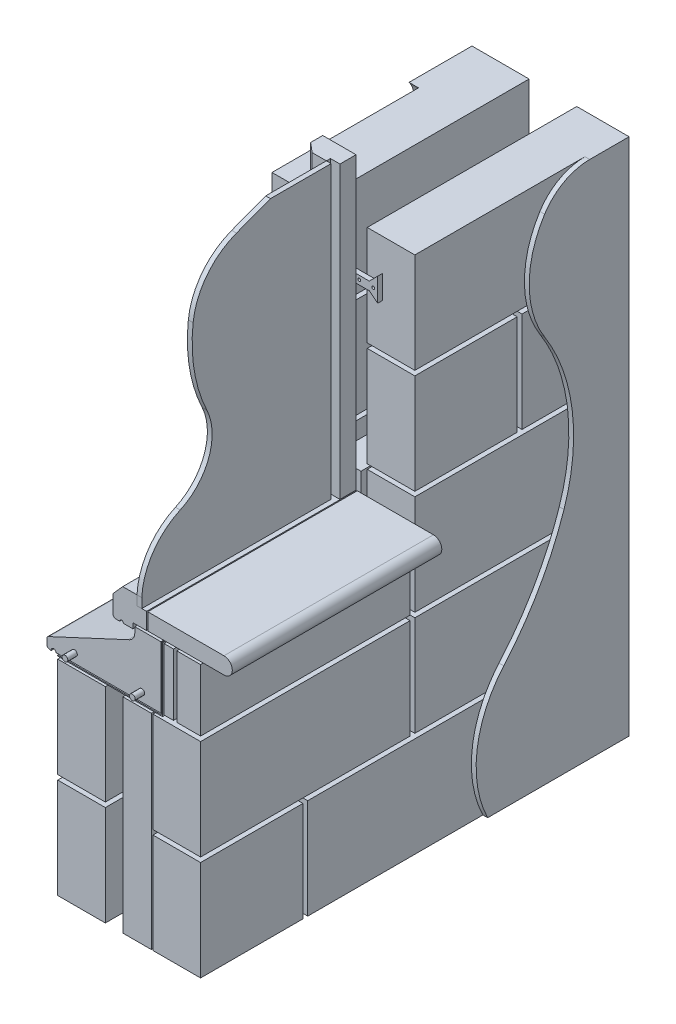
SolidWorks part; units mm, degrees
ref_plane "Front Plane" through (0, 0, 0) normal (0, 0, 1) x (1, 0, 0)
ref_plane "Top Plane" through (0, 0, 0) normal (0, 1, 0) x (1, 0, 0)
ref_plane "Right Plane" through (0, 0, 0) normal (1, 0, 0) x (0, 0, -1)
sketch "Sketch1" plane through (0, 0, 0) normal (0, 0, 1) x (1, 0, 0)
  line L1 (0, 0) -> (100, 0)
  line L2 (0, 0) -> (0, 210)
  line L3 (0, 210) -> (100, 210)
  line L4 (100, 0) -> (100, 210)
  line L5 (200, 210) -> (300, 210)
  line L6 (200, 210) -> (200, 0)
  line L7 (200, 0) -> (300, 0)
  line L8 (300, 210) -> (300, 0)
  dimension "D1" = 100
  dimension "D2" = 210
  dimension "D3" = 100
  dimension "D4" = 100
extrude "Extrude1" add sketch "Sketch1" against normal blind 440
sketch "Sketch2" plane through (0, 0, 0) normal (0, 0, 1) x (1, 0, 0)
  line L0 (0, 210) -> (0, 0) construction
  line L1 (0, -10) -> (100, -10)
  line L2 (0, -10) -> (0, -220)
  line L3 (0, -220) -> (100, -220)
  line L4 (100, -10) -> (100, -220)
  line L5 (200, -10) -> (300, -10)
  line L6 (200, -10) -> (200, -220)
  line L7 (200, -220) -> (300, -220)
  line L8 (300, -10) -> (300, -220)
  line L9 (200, 0) -> (300, 0) construction
  line L10 (0, 0) -> (100, 0) construction
  dimension "D1" = 100
  dimension "D2" = 210
  dimension "D3" = 100
  dimension "D4" = 100
  dimension "D5" = 210
  dimension "D6" = 10
  dimension "D7" = 10
extrude "Extrude2" add sketch "Sketch2" against normal blind 215
sketch "Sketch3" plane through (0, 0, 0) normal (0, 0, 1) x (1, 0, 0)
  line L0 (216.8231, 220) -> (216.8231, 350)
  line L1 (161.8231, 350) -> (161.8231, 338.3938)
  line L2 (216.8231, 220) -> (-3.7571, 220)
  line L3 (148.2215, 319.4449) -> (-18.8696, 241.5502)
  line L5 (161.8231, 350) -> (216.8231, 350)
  arc A0 (-18.8696, 241.5502) -> (-13.6311, 218.6752) centre (-13.7993, 230.674) ccw
  arc A1 (-13.6311, 218.6752) -> (-3.7571, 220) centre (-8.7517, 219.7666) cw
  arc A2 (161.8231, 338.3938) -> (148.2215, 319.4449) centre (141.8231, 338.3938) cw
  dimension "D1" = 20
  dimension "D5" = 5
  dimension "D4" = 12
  dimension "D2" = 130
  dimension "D3" = 167.0911
  dimension "D6" = 220.5803
  dimension "D8" = 55
extrude "Extrude3" add sketch "Sketch3" against normal blind 440
sketch "Sketch4" plane through (0, 0, 0) normal (0, 0, 1) x (1, 0, 0)
  line L0 (186.5077, 390.1642) -> (186.5077, 355.1642)
  line L1 (186.5077, 355.1642) -> (158.0261, 355.1642)
  line L2 (158.0261, 355.1642) -> (158.0261, 343.9747)
  line L3 (158.0261, 343.9747) -> (138.0261, 343.9747)
  line L4 (130.0261, 343.9747) -> (120.0261, 343.9747)
  line L5 (120.0261, 343.9747) -> (116.5077, 347.8035)
  line L6 (116.5077, 347.8035) -> (116.5077, 387.8035)
  line L7 (116.5077, 387.8035) -> (136.5077, 410.1642)
  line L8 (136.5077, 410.1642) -> (166.5077, 410.1642)
  line L9 (166.5077, 410.1642) -> (166.5077, 390.1642)
  line L10 (166.5077, 390.1642) -> (186.5077, 390.1642)
  arc A0 (138.0261, 343.9747) -> (130.0261, 343.9747) centre (134.0261, 343.9747) ccw
  dimension "D10" = 4
  dimension "D1" = 70
  dimension "D2" = 50
  dimension "D3" = 35
  dimension "D4" = 20
  dimension "D5" = 20
  dimension "D6" = 10
  dimension "D7" = 40
  dimension "D8" = 30
  dimension "D9" = 30
extrude "Extrude4" add sketch "Sketch4" against normal blind 440
sketch "Sketch5" plane through (0, 0, 0) normal (0, 0, 1) x (1, 0, 0)
  line L0 (300, 0) -> (300, 210) construction
  line L1 (223.1619, 350) -> (243.1619, 350)
  line L2 (223.1619, 350) -> (223.1619, 220)
  line L3 (223.1619, 220) -> (243.1619, 220)
  line L4 (243.1619, 350) -> (243.1619, 220)
  line L5 (250, 350) -> (300, 350)
  line L6 (250, 350) -> (250, 220)
  line L7 (250, 220) -> (300, 220)
  line L8 (300, 350) -> (300, 220)
  line L9 (216.8231, 350) -> (161.8231, 350) construction
  dimension "D1" = 130
  dimension "D2" = 20
  dimension "D3" = 50
extrude "Extrude5" add sketch "Sketch5" against normal blind 440
sketch "Sketch6" plane through (0, 0, 0) normal (0, 0, 1) x (1, 0, 0)
  line L0 (0, 217.6217) -> (218.3559, 217.6217)
  line L1 (218.3559, 217.6217) -> (218.3559, 350)
  line L2 (218.3559, 350) -> (220.2023, 350)
  line L3 (220.2023, 350) -> (220.2023, 215.4099)
  line L4 (220.2023, 215.4099) -> (0, 215.4099)
  line L5 (0, 215.4099) -> (0, 217.6217)
  line L6 (216.8231, 350) -> (161.8231, 350) construction
  dimension "D1" = 132.3783
  dimension "D2" = 220.2023
extrude "Extrude6" add sketch "Sketch6" against normal blind 440
sketch "Sketch7" plane through (0, 0, 0) normal (0, 0, 1) x (1, 0, 0)
  line L0 (189.1094, 355.6759) -> (189.1094, 390.6759)
  line L1 (189.1094, 390.6759) -> (349.1094, 390.6759)
  line L2 (349.1094, 355.6759) -> (189.1094, 355.6759)
  arc A0 (349.1094, 390.6759) -> (349.1094, 355.6759) centre (349.1094, 373.1759) cw
  dimension "D1" = 35
  dimension "D2" = 160
extrude "Extrude7" add sketch "Sketch7" against normal blind 440
sketch "Sketch8" plane through (0, 0, 0) normal (0, 0, 1) x (1, 0, 0)
  circle A0 centre (35.1553, 238.7881) radius 6
  circle A1 centre (176.4971, 238.7881) radius 6
  dimension "D1" = 12
  dimension "D2" = 12
sketch "Sketch14" plane through (0, 0, 0) normal (-1, 0, 0) x (0, 0, 1)
  line L0 (-215, -10) -> (-215, -220) construction
  line L1 (-225, -10) -> (-665, -10)
  line L2 (-225, -10) -> (-225, -220)
  line L3 (-225, -220) -> (-665, -220)
  line L4 (-665, -10) -> (-665, -220)
  line L5 (-215, -10) -> (0, -10) construction
  dimension "D1" = 440
  dimension "D2" = 210
  dimension "D3" = 10
extrude "Extrude13" add sketch "Sketch14" against normal blind 100
sketch "Sketch15" plane through (300, 0, 0) normal (1, 0, 0) x (0, 0, -1)
  line L1 (225, -10) -> (665, -10)
  line L2 (225, -10) -> (225, -220)
  line L3 (225, -220) -> (665, -220)
  line L4 (665, -10) -> (665, -220)
extrude "Extrude14" add sketch "Sketch15" against normal blind 100
sketch "Sketch16" plane through (0, 0, 0) normal (-1, 0, 0) x (0, 0, 1)
  line L0 (-225, -10) -> (-665, -10) construction
  line L1 (-675, -10) -> (-890, -10)
  line L2 (-675, -10) -> (-675, -220)
  line L3 (-675, -220) -> (-890, -220)
  line L4 (-890, -10) -> (-890, -220)
  line L6 (-665, -10) -> (-665, -220) construction
  dimension "D1" = 210
  dimension "D2" = 215
  dimension "D3" = 10
extrude "Extrude15" add sketch "Sketch16" against normal blind 100
sketch "Sketch17" plane through (300, 0, 0) normal (1, 0, 0) x (0, 0, -1)
  line L1 (675, -10) -> (890, -10)
  line L2 (675, -10) -> (675, -220)
  line L3 (675, -220) -> (890, -220)
  line L4 (890, -10) -> (890, -220)
extrude "Extrude16" add sketch "Sketch17" against normal blind 100
sketch "Sketch18" plane through (0, 0, 0) normal (-1, 0, 0) x (0, 0, 1)
  line L0 (-440, 210) -> (-440, 0) construction
  line L1 (-450, 210.1483) -> (-890, 210.1483)
  line L2 (-450, 210.1483) -> (-450, 0)
  line L3 (-450, 0) -> (-890, 0)
  line L4 (-890, 210.1483) -> (-890, 0)
  dimension "D1" = 440
  dimension "D2" = 10
extrude "Extrude17" add sketch "Sketch18" against normal blind 100
sketch "Sketch19" plane through (300, 0, 0) normal (1, 0, 0) x (0, 0, -1)
  line L0 (890, 0) -> (450, 0) construction
  line L1 (450, 210.1483) -> (890, 210.1483)
  line L2 (450, 210.1483) -> (450, 0)
  line L3 (450, 0) -> (890, 0)
  line L4 (890, 210.1483) -> (890, 0)
extrude "Extrude18" add sketch "Sketch19" against normal blind 100
extrude "Extrude19" add sketch "Sketch8" along normal blind 20
sketch "Sketch20" plane through (0, 0, 0) normal (-1, 0, 0) x (0, 0, 1)
  line L0 (-450, 210.1483) -> (-890, 210.1483) construction
  line L1 (-450, 430.1483) -> (-890, 430.1483)
  line L2 (-450, 430.1483) -> (-450, 220.1483)
  line L3 (-450, 220.1483) -> (-890, 220.1483)
  line L4 (-890, 430.1483) -> (-890, 220.1483)
  line L5 (-890, 210.1483) -> (-890, 0) construction
  dimension "D1" = 440
  dimension "D2" = 210
  dimension "D3" = 10
extrude "Extrude20" add sketch "Sketch20" against normal blind 100
sketch "Sketch21" plane through (300, 0, 0) normal (1, 0, 0) x (0, 0, -1)
  line L1 (450, 430.1483) -> (890, 430.1483)
  line L2 (450, 430.1483) -> (450, 220.1483)
  line L3 (450, 220.1483) -> (890, 220.1483)
  line L4 (890, 430.1483) -> (890, 220.1483)
extrude "Extrude21" add sketch "Sketch21" against normal blind 100
sketch "Sketch24" plane through (0, 0, 0) normal (0, 0, 1) x (1, 0, 0)
  line L1 (196.8296, 209.833) -> (136.8296, 209.833)
  line L2 (196.8296, 209.833) -> (196.8296, -220)
  line L3 (196.8296, -220) -> (136.8296, -220)
  line L4 (136.8296, 209.833) -> (136.8296, -220)
  dimension "D1" = 429.833
  dimension "D2" = 60
extrude "Extrude23" add sketch "Sketch24" against normal blind 440
sketch "Sketch25" plane through (0, 0, -890) normal (0, 0, -1) x (-1, 0, 0)
  line L1 (-196.8296, -220) -> (-136.5077, -220)
  line L2 (-196.8296, -220) -> (-196.8296, 430.1483)
  line L3 (-196.8296, 430.1483) -> (-136.5077, 430.1483)
  line L4 (-136.5077, -220) -> (-136.5077, 430.1483)
extrude "Extrude26" add sketch "Sketch25" against normal up to surface (450 mm away) up to face at (166.8296, -5.0835, -440)
sketch "Sketch26" plane through (0, 0, 0) normal (-1, 0, 0) x (0, 0, 1)
  line L0 (-890, 430.1483) -> (-890, 220.1483) construction
  line L1 (-450, 440.1483) -> (-665, 440.1483)
  line L2 (-450, 440.1483) -> (-450, 650.1483)
  line L3 (-450, 650.1483) -> (-665, 650.1483)
  line L4 (-665, 440.1483) -> (-665, 650.1483)
  line L5 (-675, 440.1483) -> (-890, 440.1483)
  line L6 (-675, 440.1483) -> (-675, 650.1483)
  line L7 (-675, 650.1483) -> (-890, 650.1483)
  line L8 (-890, 440.1483) -> (-890, 650.1483)
  line L9 (-450, 430.1483) -> (-890, 430.1483) construction
  dimension "D1" = 210
  dimension "D2" = 215
  dimension "D3" = 215
  dimension "D4" = 210
  dimension "D5" = 10
  dimension "D6" = 10
extrude "Extrude27" add sketch "Sketch26" against normal blind 100
sketch "Sketch28" plane through (300, 0, 0) normal (1, 0, 0) x (0, 0, -1)
  line L1 (450, 650.1483) -> (665, 650.1483)
  line L2 (450, 650.1483) -> (450, 440.1483)
  line L3 (450, 440.1483) -> (665, 440.1483)
  line L4 (665, 650.1483) -> (665, 440.1483)
  line L5 (675, 650.1483) -> (890, 650.1483)
  line L6 (675, 650.1483) -> (675, 440.1483)
  line L7 (675, 440.1483) -> (890, 440.1483)
  line L8 (890, 650.1483) -> (890, 440.1483)
extrude "Extrude29" add sketch "Sketch28" against normal blind 100
sketch "Sketch29" plane through (0, 0, 0) normal (-1, 0, 0) x (0, 0, 1)
  line L0 (-675, 650.1483) -> (-890, 650.1483) construction
  line L1 (-890, 660.1483) -> (-450, 660.1483)
  line L2 (-890, 660.1483) -> (-890, 870.1483)
  line L3 (-890, 870.1483) -> (-450, 870.1483)
  line L4 (-450, 660.1483) -> (-450, 870.1483)
  dimension "D1" = 210
  dimension "D2" = 440
  dimension "D3" = 10
extrude "Extrude30" add sketch "Sketch29" against normal blind 100
sketch "Sketch30" plane through (300, 0, 0) normal (1, 0, 0) x (0, 0, -1)
  line L1 (450, 870.1483) -> (890, 870.1483)
  line L2 (450, 870.1483) -> (450, 660.1483)
  line L3 (450, 660.1483) -> (890, 660.1483)
  line L4 (890, 870.1483) -> (890, 660.1483)
extrude "Extrude31" add sketch "Sketch30" against normal blind 100
ref_plane "Plane1" through (0, 390.6759, 0) normal (0, 1, 0) x (-1, 0, 0)
sketch "Sketch31" plane through (0, 390.6759, 0) normal (0, 1, 0) x (-1, 0, 0)
  line L0 (-116.5077, -440) -> (-116.5077, -414.6101)
  line L1 (-116.5077, -440) -> (-116.5077, 0) construction
  line L2 (-116.5077, -414.6101) -> (-136.5077, -397.7493)
  line L3 (-136.5077, -440) -> (-136.5077, 0) construction
  line L4 (-136.5077, -397.7493) -> (-166.5077, -397.7493)
  line L5 (-166.5077, -440) -> (-166.5077, 0) construction
  line L6 (-166.5077, -397.7493) -> (-166.5077, -406.1797)
  line L7 (-166.5077, -406.1797) -> (-186.5077, -406.1797)
  line L8 (-186.5077, -440) -> (-186.5077, 0) construction
  line L9 (-186.5077, -406.1797) -> (-186.5077, -440)
  line L10 (-136.5077, -440) -> (-196.8296, -440) construction
  line L11 (-186.5077, -440) -> (-116.5077, -440)
extrude "Extrude32" add sketch "Sketch31" along normal blind 610
sketch "Sketch32" plane through (166.5077, 0, 0) normal (1, 0, 0) x (0, 0, -1)
  line L0 (440, 390.1642) -> (0, 390.1642) construction
  line L1 (397.7493, 1000.6759) -> (0, 1000.6759)
  line L2 (397.7493, 1000.6759) -> (397.7493, 390.1642)
  line L3 (397.7493, 390.1642) -> (0, 390.1642)
  line L4 (0, 1000.6759) -> (0, 390.1642)
extrude "Extrude35" add sketch "Sketch32" along normal blind 10 separate body
sketch "Sketch33" plane through (0, 0, 0) normal (-1, 0, 0) x (0, 0, 1)
  line L0 (-890, 870.1483) -> (-890, -220)
  line L1 (-890, -220) -> (-717.0937, -220)
  line L2 (-890, -220) -> (-675, -220) construction
  line L3 (-717.0937, -220) -> (-717.0937, -105.0186)
  line L4 (-450, 430.1483) -> (-890, 430.1483) construction
  line L5 (-450, 870.1483) -> (-890, 870.1483) construction
  line L6 (-757.7152, 870.1483) -> (-890, 870.1483)
  arc A0 (-717.0937, -105.0186) -> (-757.7152, 136.4536) centre (-1455.1135, -105.0186) ccw
  arc A1 (-757.7152, 136.4536) -> (-727.3199, 430.1483) centre (-427.7018, 250.7198) cw
  arc A2 (-727.3199, 430.1483) -> (-757.7152, 815.7352) centre (-1013.5756, 601.5746) ccw
  arc A3 (-757.7152, 815.7352) -> (-757.7152, 870.1483) centre (-725.2112, 842.9418) cw
extrude "Extrude36" add sketch "Sketch33" along normal blind 40
sketch "Sketch34" plane through (0, 0, -717.0937) normal (0, 0, 1) x (1, 0, 0)
  line L0 (-40, -220) -> (-24.3646, -152.4104)
  line L1 (-24.3646, -152.4104) -> (-20, 870.1483)
  line L2 (-40, 870.1483) -> (0, 870.1483) construction
extrude "Cut-Extrude1" cut sketch "Sketch34" against normal through all and the other way through all
sketch "Sketch35" plane through (0, 0, -440) normal (0, 0, -1) x (-1, 0, 0)
  line L0 (-214.2474, 784.7048) -> (-84.9095, 784.7048)
  line L2 (-214.2474, 784.7048) -> (-231.8139, 802.2713)
  line L3 (-231.8139, 802.2713) -> (-231.8139, 753.0852)
  line L4 (-231.8139, 753.0852) -> (-214.2474, 767.1384)
  line L5 (-84.9095, 784.7048) -> (-67.343, 802.2713)
  line L6 (-67.343, 802.2713) -> (-67.343, 753.0852)
  line L8 (-67.343, 753.0852) -> (-84.9095, 767.1384)
  line L9 (-84.9095, 767.1384) -> (-214.2474, 767.1384)
  circle A0 centre (-222.625, 776.6988) radius 3
  circle A1 centre (-193.2693, 776.6988) radius 3
  circle A2 centre (-150.3194, 776.6988) radius 3
  circle A3 centre (-108.9457, 776.6988) radius 3
  circle A4 centre (-76.0437, 776.6988) radius 3
  dimension "D1" = 6
  dimension "D2" = 6
  dimension "D3" = 6
  dimension "D4" = 6
  dimension "D5" = 6
  dimension "D6" = 129.3379
  dimension "D7" = 17.5665
  dimension "D8" = 49.1861
extrude "Extrude37" add sketch "Sketch35" along normal blind 10 separate body
sketch "Sketch36" plane through (166.5077, 0, 0) normal (-1, 0, 0) x (0, 0, 1)
  line L0 (-270.2573, 1000.6759) -> (-198.8747, 973.7077)
  line L1 (-397.7493, 1000.6759) -> (0, 1000.6759) construction
  line L2 (-270.2573, 1000.6759) -> (0, 1000.6759)
  line L3 (0, 1000.6759) -> (0, 410.1642)
  arc A0 (-198.8747, 973.7077) -> (-107.7713, 856.3567) centre (-249.1468, 840.6411) cw
  arc A1 (-107.7713, 856.3567) -> (-136.7857, 682.587) centre (-428.8667, 820.663) cw
  arc A2 (-136.7857, 682.587) -> (-80.6903, 529.128) centre (-33.0222, 633.5347) ccw
  arc A3 (-80.6903, 529.128) -> (0, 410.1642) centre (-138.1287, 403.3219) cw
extrude "Cut-Extrude3" cut sketch "Sketch36" against normal up to next (10 mm away)
sketch "Sketch37" plane through (300, 0, 0) normal (1, 0, 0) x (0, 0, -1)
  line L0 (890, -220) -> (890, 870.1483)
  line L1 (890, 870.1483) -> (807.3637, 870.1483)
  line L2 (890, 870.1483) -> (450, 870.1483) construction
  line L3 (225, -220) -> (665, -220) construction
  line L4 (592.9725, -220) -> (890, -220)
  arc A0 (807.3637, 870.1483) -> (712.5802, 817.992) centre (807.3637, 757.9453) ccw
  arc A1 (712.5802, 817.992) -> (712.5802, 594.5737) centre (888.9129, 706.2829) ccw
  arc A2 (712.5802, 594.5737) -> (753.2708, 260.5748) centre (381.3647, 384.7442) cw
  arc A3 (753.2708, 260.5748) -> (626.8237, 39.4133) centre (136.4228, 466.5237) cw
  arc A4 (626.8237, 39.4133) -> (592.9725, -220) centre (804.9794, -115.7498) ccw
extrude "Extrude38" add sketch "Sketch37" along normal blind 10
